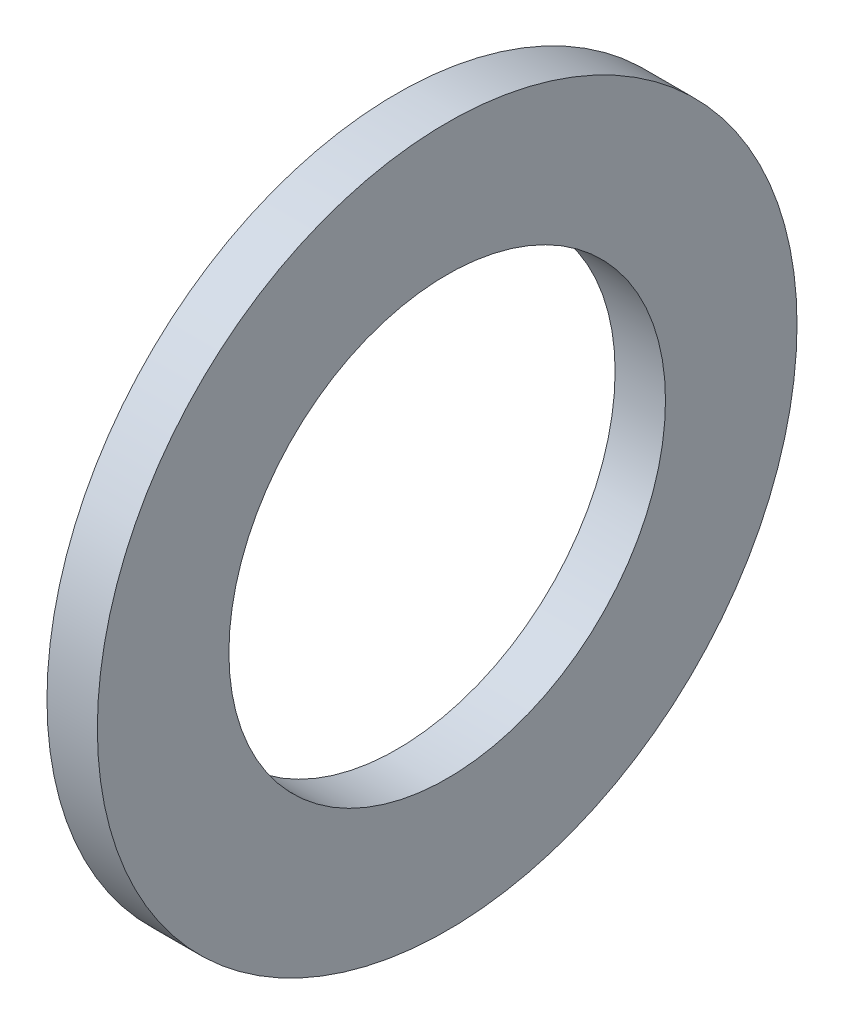
SolidWorks part; units mm, degrees
ref_plane "Front Plane" through (0, 0, 0) normal (0, 0, 1) x (1, 0, 0)
ref_plane "Top Plane" through (0, 0, 0) normal (0, 1, 0) x (1, 0, 0)
ref_plane "Right Plane" through (0, 0, 0) normal (1, 0, 0) x (0, 0, -1)
sketch "Sketch1" plane through (0, 0, 0) normal (1, 0, 0) x (0, 0, -1)
  circle A0 centre (0, 0) radius 6.35
  circle A1 centre (0, 0) radius 3.9624
  dimension "OD" = 12.7
  dimension "ID" = 7.9248
extrude "Boss-Extrude1" add sketch "Sketch1" along normal blind 0.9144
